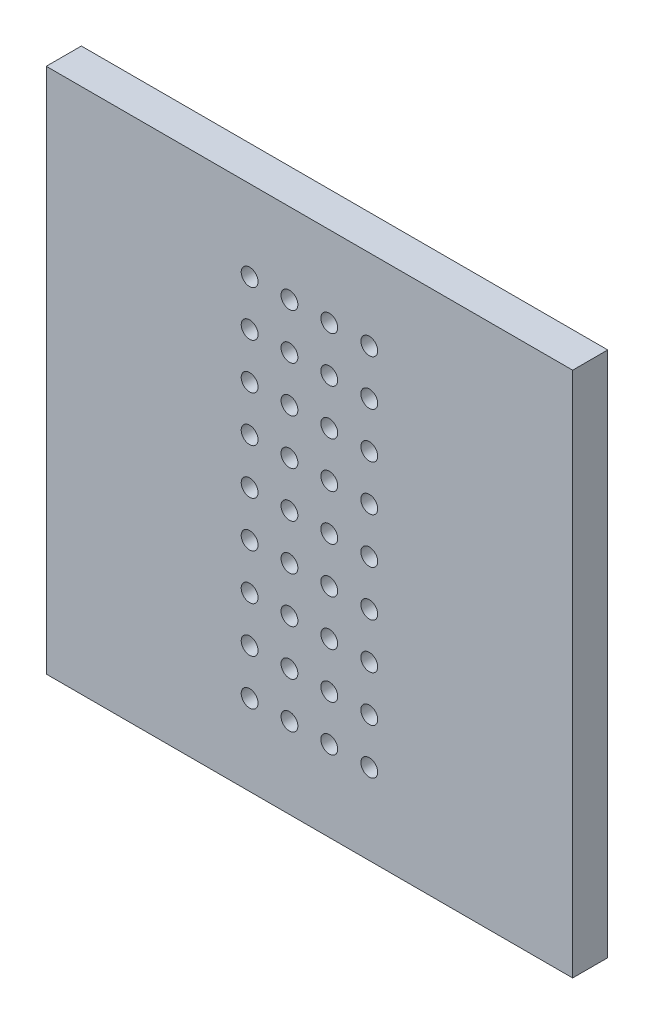
SolidWorks part; units mm, degrees
ref_plane "Plan de face" through (0, 0, 0) normal (0, 0, 1) x (1, 0, 0)
ref_plane "Plan de dessus" through (0, 0, 0) normal (0, 1, 0) x (1, 0, 0)
ref_plane "Plan de droite" through (0, 0, 0) normal (1, 0, 0) x (0, 0, -1)
sketch "Esquisse1" plane through (0, 0, 0) normal (0, 0, 1) x (1, 0, 0)
  line L1 (-15, -15) -> (15, -15)
  line L2 (-15, -15) -> (-15, 15)
  line L3 (-15, 15) -> (15, 15)
  line L4 (15, -15) -> (15, 15)
  line L5 (-15, -15) -> (15, 15) construction
  line L6 (-15, 15) -> (15, -15) construction
  point P0 (0, 0)
extrude "Base_Plate" add sketch "Esquisse1" along normal blind 2
sketch "Sketch_Perforations" plane through (0, 0, 2) normal (0, 0, 1) x (1, 0, 0)
  circle A0 centre (-3.41, -10.4) radius 0.48
  circle A1 centre (-3.41, -7.8) radius 0.48
  circle A2 centre (-3.41, -5.2) radius 0.48
  circle A3 centre (-3.41, -2.6) radius 0.48
  circle A4 centre (-3.41, 0) radius 0.48
  circle A5 centre (-3.41, 2.6) radius 0.48
  circle A6 centre (-3.41, 5.2) radius 0.48
  circle A7 centre (-3.41, 7.8) radius 0.48
  circle A8 centre (-3.41, 10.4) radius 0.48
  circle A9 centre (-1.14, -10.4) radius 0.48
  circle A10 centre (-1.14, -7.8) radius 0.48
  circle A11 centre (-1.14, -5.2) radius 0.48
  circle A12 centre (-1.14, -2.6) radius 0.48
  circle A13 centre (-1.14, 0) radius 0.48
  circle A14 centre (-1.14, 2.6) radius 0.48
  circle A15 centre (-1.14, 5.2) radius 0.48
  circle A16 centre (-1.14, 7.8) radius 0.48
  circle A17 centre (-1.14, 10.4) radius 0.48
  circle A18 centre (1.13, -10.4) radius 0.48
  circle A19 centre (1.13, -7.8) radius 0.48
  circle A20 centre (1.13, -5.2) radius 0.48
  circle A21 centre (1.13, -2.6) radius 0.48
  circle A22 centre (1.13, 0) radius 0.48
  circle A23 centre (1.13, 2.6) radius 0.48
  circle A24 centre (1.13, 5.2) radius 0.48
  circle A25 centre (1.13, 7.8) radius 0.48
  circle A26 centre (1.13, 10.4) radius 0.48
  circle A27 centre (3.41, -10.4) radius 0.48
  circle A28 centre (3.41, -7.8) radius 0.48
  circle A29 centre (3.41, -5.2) radius 0.48
  circle A30 centre (3.41, -2.6) radius 0.48
  circle A31 centre (3.41, 0) radius 0.48
  circle A32 centre (3.41, 2.6) radius 0.48
  circle A33 centre (3.41, 5.2) radius 0.48
  circle A34 centre (3.41, 7.8) radius 0.48
  circle A35 centre (3.41, 10.4) radius 0.48
extrude "Cut_Perforations" cut sketch "Sketch_Perforations" against normal blind 10
